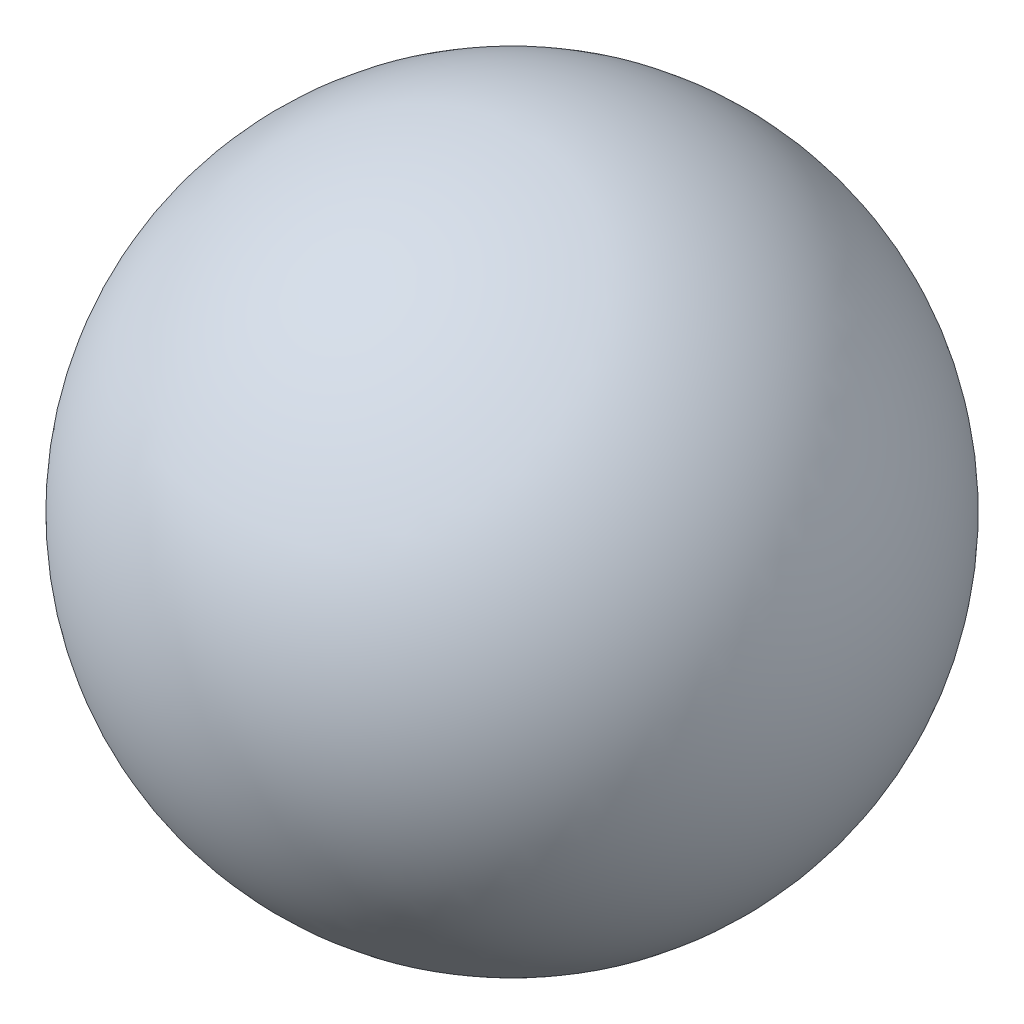
SolidWorks part; units mm, degrees
ref_plane "Front Plane" through (0, 0, 0) normal (0, 0, 1) x (1, 0, 0)
ref_plane "Top Plane" through (0, 0, 0) normal (0, 1, 0) x (1, 0, 0)
ref_plane "Right Plane" through (0, 0, 0) normal (1, 0, 0) x (0, 0, -1)
sketch "Sketch1" plane through (0, 0, 0) normal (0, 0, 1) x (1, 0, 0)
  line L0 (0, 120.65) -> (0, -120.65)
  arc A0 (0, 120.65) -> (0, -120.65) centre (0, 0) ccw
  dimension "D1" = 241.3
revolve "Revolve1" add sketch "Sketch1" angle 360 about L0
